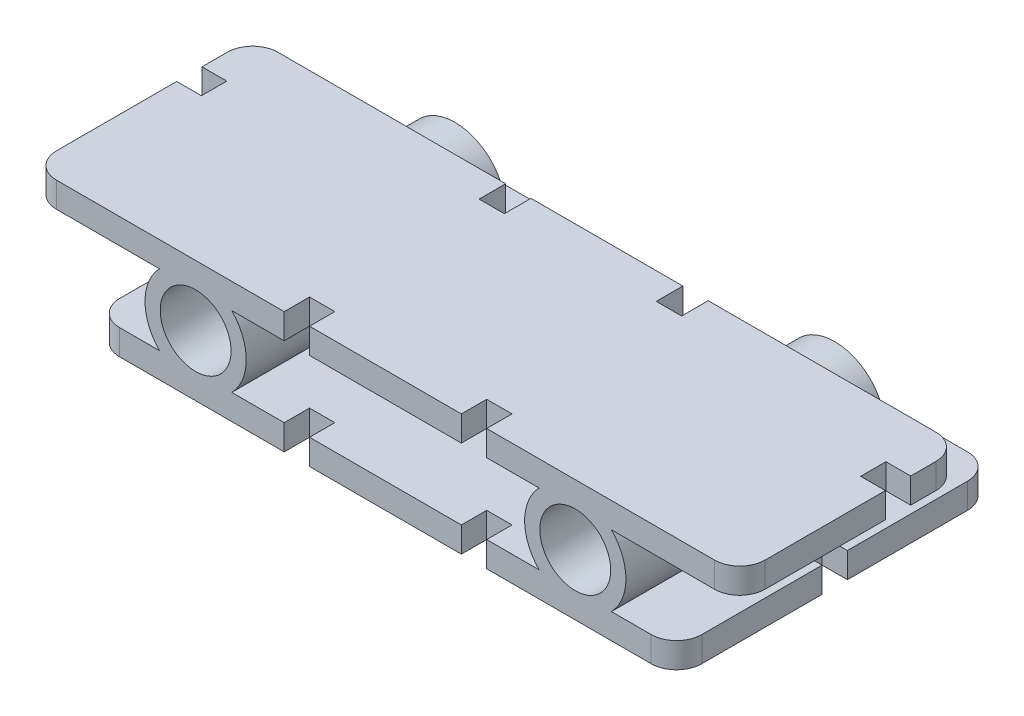
SolidWorks part; units mm, degrees
ref_plane "Front Plane" through (0, 0, 0) normal (0, 0, 1) x (1, 0, 0)
ref_plane "Top Plane" through (0, 0, 0) normal (0, 1, 0) x (1, 0, 0)
ref_plane "Right Plane" through (0, 0, 0) normal (1, 0, 0) x (0, 0, -1)
sketch "Sketch1" plane through (0, 0, 0) normal (0, 1, 0) x (1, 0, 0)
  line L1 (-29.21, -15.875) -> (29.21, -15.875)
  line L2 (-29.21, -15.875) -> (-29.21, 15.875)
  line L3 (-29.21, 15.875) -> (29.21, 15.875)
  line L4 (29.21, -15.875) -> (29.21, 15.875)
  line L5 (-29.21, -15.875) -> (29.21, 15.875) construction
  line L6 (-29.21, 15.875) -> (29.21, -15.875) construction
  point P0 (0, 0)
  dimension "D1" = 58.42
  dimension "D2" = 31.75
extrude "Boss-Extrude1" add sketch "Sketch1" along normal blind 2.54
fillet "Fillet1" radius 2.54 4 edges at (29.21, 1.27, 15.875) (29.21, 1.27, -15.875) (-29.21, 1.27, -15.875) (-29.21, 1.27, 15.875)
sketch "Sketch4" plane through (0, 0, 0) normal (0, 0, 1) x (1, 0, 0)
  line L0 (0, -1.397) -> (0, 1.397) construction
  circle A0 centre (-19.05, 6.096) radius 5.08
  circle A1 centre (19.05, 6.096) radius 5.08
extrude "Boss-Extrude3" add sketch "Sketch4" along normal blind 15.875
sketch "Sketch5" plane through (0, 0, 0) normal (0, 0, -1) x (-1, 0, 0)
  circle A0 centre (-19.05, 6.096) radius 5.08
  circle A1 centre (19.05, 6.096) radius 5.08
extrude "Boss-Extrude4" add sketch "Sketch5" along normal blind 10.16
sketch "Sketch6" plane through (0, 0, 15.875) normal (0, 0, 1) x (1, 0, 0)
  line L0 (0, -1.397) -> (0, 1.397) construction
  circle A0 centre (-19.05, 6.096) radius 3.556
  circle A1 centre (19.05, 6.096) radius 3.556
extrude "Cut-Extrude2" cut sketch "Sketch6" against normal through all
sketch "Sketch9" plane through (0, 2.54, 0) normal (0, 1, 0) x (1, 0, 0)
  line L0 (26.67, 15.875) -> (-26.67, 15.875) construction
  line L1 (-13.97, 15.875) -> (13.97, 15.875)
  line L2 (0, 15.875) -> (0, 12.065)
  line L3 (-13.97, 12.065) -> (13.97, 12.065)
  line L4 (13.97, 15.875) -> (13.97, 12.065)
  line L5 (-13.97, 15.875) -> (-13.97, 12.065)
  line M5 (26.67, 15.875) -> (-26.67, 15.875)
  dimension "D1" = 3.81
  dimension "D2" = 13.97
extrude "Cut-Extrude4" cut sketch "Sketch9" against normal blind 1.27 contours L1 L5 L3 L2 | L4 L2 L3 M5
sketch "Sketch10" plane through (0, 0, 0) normal (0, 1, 0) x (1, 0, 0)
  line L0 (-29.21, 13.335) -> (-29.21, -13.335) construction
  line L12 (-29.21, 0) -> (-26.67, 0)
  line L13 (-29.21, -1.27) -> (-29.21, 1.27)
  line L14 (-29.21, 1.27) -> (-26.67, 1.27)
  line L15 (-26.67, -1.27) -> (-26.67, 1.27)
  line L16 (-29.21, -1.27) -> (-26.67, -1.27)
  line L17 (0, -6.1468) -> (0, 6.1468) construction
  line L18 (29.21, -1.27) -> (26.67, -1.27)
  line L19 (29.21, -1.27) -> (29.21, 1.27)
  line L20 (29.21, 1.27) -> (26.67, 1.27)
  line L21 (26.67, -1.27) -> (26.67, 1.27)
  line L22 (29.21, 0) -> (26.67, 0)
  line L23 (-7.62, 15.875) -> (-10.16, 15.875)
  line L24 (-7.62, 15.875) -> (-7.62, 13.335)
  line L25 (-7.62, 13.335) -> (-10.16, 13.335)
  line L26 (-10.16, 15.875) -> (-10.16, 13.335)
  line L27 (-6.1468, 0) -> (6.1468, 0) construction
  line L28 (-7.62, -13.335) -> (-10.16, -13.335)
  line L29 (-10.16, -15.875) -> (-10.16, -13.335)
  line L30 (-7.62, -15.875) -> (-10.16, -15.875)
  line L31 (-7.62, -15.875) -> (-7.62, -13.335)
  line L32 (7.62, -15.875) -> (7.62, -13.335)
  line L33 (7.62, -15.875) -> (10.16, -15.875)
  line L34 (10.16, -15.875) -> (10.16, -13.335)
  line L35 (7.62, -13.335) -> (10.16, -13.335)
  line L36 (7.62, 13.335) -> (10.16, 13.335)
  line L37 (10.16, 15.875) -> (10.16, 13.335)
  line L38 (7.62, 15.875) -> (10.16, 15.875)
  line L39 (7.62, 15.875) -> (7.62, 13.335)
  line L40 (26.67, 15.875) -> (-26.67, 15.875) construction
  line L41 (-3.81, 19.685) -> (3.81, 19.685)
  line L42 (-3.81, 19.685) -> (-3.81, 12.065)
  line L43 (-3.81, 12.065) -> (3.81, 12.065)
  line L44 (3.81, 19.685) -> (3.81, 12.065)
  line L45 (-3.81, 19.685) -> (3.81, 12.065) construction
  line L46 (-3.81, 12.065) -> (3.81, 19.685) construction
  line L47 (-13.97, 12.065) -> (13.97, 12.065) construction
  line L48 (-10.16, 15.875) -> (10.16, 15.875)
  line L49 (-10.16, 15.875) -> (-10.16, 12.065)
  line L50 (-10.16, 12.065) -> (10.16, 12.065)
  line L51 (10.16, 15.875) -> (10.16, 12.065)
  point P34 (0, 15.875)
  dimension "D1" = 2.54
  dimension "D2" = 2.54
  dimension "D3" = 1.27
  dimension "D4" = 2.54
  dimension "D5" = 7.62
  dimension "D6" = 7.62
extrude "Cut-Extrude6" cut sketch "Sketch10" along normal through all
sketch "Sketch11" plane through (0, 0, 0) normal (0, 0, 1) x (1, 0, 0)
  line L0 (-7.62, 2.54) -> (7.62, 2.54) construction
  line L1 (-35.56, 9.652) -> (35.56, 9.652)
  line L2 (-35.56, 9.652) -> (-35.56, 12.192)
  line L3 (-35.56, 12.192) -> (35.56, 12.192)
  line L4 (35.56, 9.652) -> (35.56, 12.192)
  line L5 (-26.67, 1.27) -> (26.67, 3.81) construction
  line L6 (-26.67, 3.81) -> (26.67, 1.27) construction
  point P0 (0, 2.54)
  dimension "D1" = 71.12
  dimension "D2" = 2.54
extrude "Boss-Extrude5" add sketch "Sketch11" along normal up to surface (15.875 mm away) up to face at (-15.494, 6.096, 15.875)
sketch "Sketch12" plane through (0, 0, 0) normal (0, 0, -1) x (-1, 0, 0)
  line L0 (15.4222, 9.652) -> (-15.4222, 9.652) construction
  line L1 (-35.56, 9.652) -> (35.56, 9.652)
  line L2 (-35.56, 9.652) -> (-35.56, 12.192)
  line L3 (-35.56, 12.192) -> (35.56, 12.192)
  line L4 (35.56, 9.652) -> (35.56, 12.192)
  point P0 (0, 9.652)
  dimension "D1" = 2.54
  dimension "D2" = 71.12
extrude "Boss-Extrude6" add sketch "Sketch12" along normal blind 6.35
fillet "Fillet2" radius 2.54 4 edges at (35.56, 10.922, -6.35) (35.56, 10.922, 15.875) (-35.56, 10.922, -6.35) (-35.56, 10.922, 15.875)
ref_plane "Plane1" through (0, 0, 4.826) normal (0, 0, 1) x (1, 0, 0)
sketch "Sketch13" plane through (0, 12.192, 0) normal (0, 1, 0) x (1, 0, 0)
  line L0 (-35.615, -1.2661) -> (-33.075, -1.2661)
  line L1 (7.62, -15.875) -> (10.16, -15.875)
  line L2 (7.62, -15.875) -> (7.62, -13.335)
  line L3 (7.62, -13.335) -> (10.16, -13.335)
  line L4 (10.16, -15.875) -> (10.16, -13.335)
  line L5 (0, -6.7056) -> (0, 6.7056) construction
  line L6 (-7.62, -13.335) -> (-10.16, -13.335)
  line L7 (-10.16, -15.875) -> (-10.16, -13.335)
  line L8 (-7.62, -15.875) -> (-10.16, -15.875)
  line L9 (-7.62, -15.875) -> (-7.62, -13.335)
  line L10 (-33.075, 1.2739) -> (-33.075, -1.2661)
  line L11 (35.615, 1.2739) -> (33.075, 1.2739)
  line L12 (35.615, 1.2739) -> (35.615, -1.2661)
  line L13 (35.615, -1.2661) -> (33.075, -1.2661)
  line L14 (33.075, 1.2739) -> (33.075, -1.2661)
  line L15 (-35.615, 1.2739) -> (-33.075, 1.2739)
  line L16 (-35.615, 1.2739) -> (-35.615, -1.2661)
  line L17 (-6.7056, -4.826) -> (6.7056, -4.826) construction
  line L18 (7.62, 3.683) -> (10.16, 3.683)
  line L19 (10.16, 6.223) -> (10.16, 3.683)
  line L20 (7.62, 6.223) -> (10.16, 6.223)
  line L21 (7.62, 6.223) -> (7.62, 3.683)
  line L22 (-7.62, 6.223) -> (-7.62, 3.683)
  line L23 (-7.62, 6.223) -> (-10.16, 6.223)
  line L24 (-10.16, 6.223) -> (-10.16, 3.683)
  line L25 (-7.62, 3.683) -> (-10.16, 3.683)
  dimension "D1" = 2.54
  dimension "D2" = 2.54
  dimension "D3" = 2.54
extrude "Cut-Extrude7" cut sketch "Sketch13" against normal blind 2.54
sketch "Sketch14" plane through (0, 0, -3.683) normal (0, 0, -1) x (-1, 0, 0)
  line L1 (10.16, 12.192) -> (7.62, 12.192)
  line L2 (10.16, 12.192) -> (10.16, 9.652)
  line L3 (10.16, 9.652) -> (7.62, 9.652)
  line L4 (7.62, 12.192) -> (7.62, 9.652)
  line L5 (-7.62, 9.652) -> (-10.166, 9.652)
  line L6 (-7.62, 9.652) -> (-7.62, 12.192)
  line L7 (-7.62, 12.192) -> (-10.166, 12.192)
  line L8 (-10.166, 9.652) -> (-10.166, 12.192)
extrude "Cut-Extrude8" cut sketch "Sketch14" along normal through all
